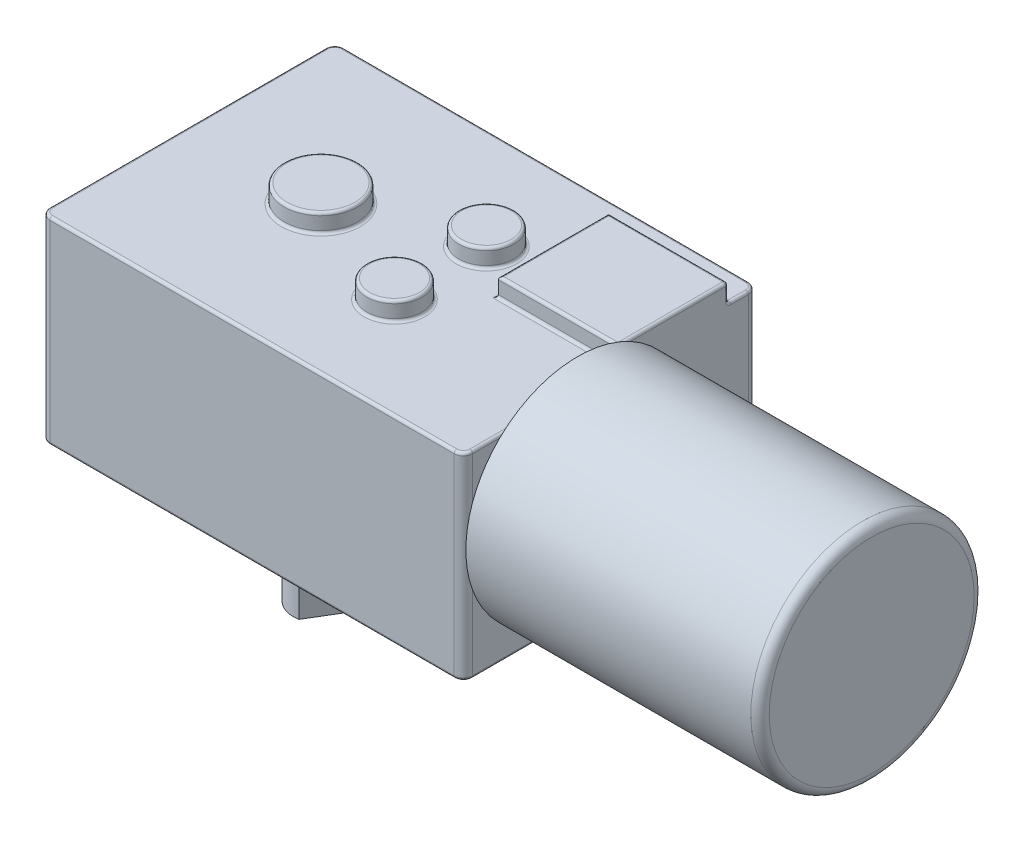
SolidWorks part; units mm, degrees
ref_plane "Front Plane" through (0, 0, 0) normal (0, 0, 1) x (1, 0, 0)
ref_plane "Top Plane" through (0, 0, 0) normal (0, 1, 0) x (1, 0, 0)
ref_plane "Right Plane" through (0, 0, 0) normal (1, 0, 0) x (0, 0, -1)
sketch "Sketch1" plane through (0, 0, 0) normal (0, 1, 0) x (1, 0, 0)
  line L1 (-23, 16) -> (23, 16)
  line L2 (-23, 16) -> (-23, -16)
  line L3 (-23, -16) -> (23, -16)
  line L4 (23, 16) -> (23, -16)
  line L5 (-23, 16) -> (23, -16) construction
  line L6 (-23, -16) -> (23, 16) construction
  point P0 (0, 0)
  dimension "D1" = 32
  dimension "D2" = 46
extrude "Boss-Extrude1" add sketch "Sketch1" along normal blind 21.5
fillet "Fillet1" radius 1 4 edges at (-23, 10.75, -16) (-23, 10.75, 16) (23, 10.75, -16) (23, 10.75, 16)
sketch "Sketch2" plane through (0, 21.5, 0) normal (0, 1, 0) x (1, 0, 0)
  line L0 (23, -15) -> (23, 15) construction
  line L1 (23, 12.8) -> (10, 12.8)
  line L2 (23, 12.8) -> (23, 0.8)
  line L3 (23, 0.8) -> (10, 0.8)
  line L4 (10, 12.8) -> (10, 0.8)
  line L5 (22, 16) -> (-22, 16) construction
  dimension "D1" = 3.2
  dimension "D2" = 12
  dimension "D3" = 13
extrude "Boss-Extrude2" add sketch "Sketch2" along normal blind 2
sketch "Sketch3" plane through (0, 21.5, 0) normal (0, 1, 0) x (1, 0, 0)
  line L0 (-23, 0) -> (-8.5, 0) construction
  line L1 (-23, 15) -> (-23, -15) construction
  line L3 (-8.5, 0) -> (4.5, 0) construction
  line L4 (4.5, 0) -> (4.5, 5) construction
  line L5 (4.5, 0) -> (4.5, -5) construction
  circle A0 centre (-8.5, 0) radius 4
  circle A1 centre (4.5, 5) radius 3
  circle A2 centre (4.5, -5) radius 3
  dimension "D2" = 8
  dimension "D3" = 6
  dimension "D4" = 6
  dimension "D1" = 14.5
  dimension "D5" = 13
  dimension "D6" = 5
  dimension "D7" = 5
extrude "Boss-Extrude3" add sketch "Sketch3" along normal blind 2
sketch "Sketch4" plane through (0, 0, 0) normal (0, -1, 0) x (1, 0, 0)
  line L0 (-23, 0) -> (-8.5, 0) construction
  line L1 (-23, -15) -> (-23, 15) construction
  line L2 (-16.4, 9.4) -> (16.4, 9.4) construction
  line L3 (16.4, 9.4) -> (16.4, -9.4) construction
  line L4 (16.4, -9.4) -> (-16.4, -9.4) construction
  line L5 (-16.4, -9.4) -> (-16.4, 9.4) construction
  line L6 (-22, 16) -> (22, 16) construction
  line L7 (23, 15) -> (23, -15) construction
  line L8 (22, -16) -> (-22, -16) construction
  circle A0 centre (-8.5, 0) radius 6.75
  circle A1 centre (-16.4, 9.4) radius 4
  circle A2 centre (-16.4, 9.4) radius 1.5
  circle A3 centre (-16.4, -9.4) radius 4
  circle A4 centre (-16.4, -9.4) radius 1.5
  circle A6 centre (16.4, -9.4) radius 1.5
  circle A7 centre (16.4, -9.4) radius 4
  circle A8 centre (16.4, 9.4) radius 1.5
  circle A9 centre (16.4, 9.4) radius 4
  circle A10 centre (4.5, 5) radius 3
  circle A11 centre (4.5, -5) radius 3
  dimension "D2" = 13.5
  dimension "D7" = 3
  dimension "D8" = 8
  dimension "D9" = 8
  dimension "D10" = 3
  dimension "D11" = 3
  dimension "D12" = 8
  dimension "D13" = 3
  dimension "D14" = 8
  dimension "D1" = 14.5
  dimension "D3" = 6.6
  dimension "D4" = 6.6
  dimension "D5" = 6.6
  dimension "D6" = 6.6
  dimension "D15" = 32.8
  dimension "D16" = 18.8
  dimension "D17" = 8.5
extrude "Boss-Extrude4" add sketch "Sketch4" along normal blind 2
fillet "Fillet2" radius 0.3 49 edges at (23, 22.5, -0.8) (23, 22.5, -12.8) (4.5, 23.5, 8) (16.5, 23.5, -0.8) (10, 23.5, -6.8) (16.5, 23.5, -12.8) (23, 23.5, -6.8) (4.5, 23.5, -2) (-8.5, 23.5, 4) (-16.4, -2, -10.9) (-16.4, -2, -13.4) (16.4, -2, -10.9) (16.4, -2, -13.4) (16.4, -2, 7.9) (16.4, -2, 5.4) (4.5, -2, -8) (4.5, -2, 2) (-16.4, -2, 7.9) (-16.4, -2, 5.4) (-22.7071, 0, 15.7071) (0, 0, 16) (22.7071, 0, 15.7071) (23, 0, 0) (22.7071, 0, -15.7071) (0, 0, -16) (-22.7071, 0, -15.7071) (-23, 0, 0) (-8.5, 0, -6.75) (-16.4, 0, 13.4) (-16.4, 0, -5.4) (16.4, 0, -5.4) (16.4, 0, 13.4) (4.5, 0, 8) (4.5, 0, -2) (23, 21.5, 7.1) (22.7071, 21.5, 15.7071) (0, 21.5, 16) (-22.7071, 21.5, 15.7071) (-23, 21.5, 0) (-22.7071, 21.5, -15.7071) (0, 21.5, -16) (22.7071, 21.5, -15.7071) (23, 21.5, -13.9) (16.5, 21.5, -12.8) (10, 21.5, -6.8) (16.5, 21.5, -0.8) (-8.5, 21.5, 4) (4.5, 21.5, -2) (4.5, 21.5, 8)
sketch "Sketch5" plane through (23, 0, 0) normal (1, 0, 0) x (0, 0, -1)
  line L0 (-3.584, 12.5) -> (0, 12.5) construction
  line L1 (0, 12.5) -> (0, 0) construction
  circle A0 centre (-3.584, 12.5) radius 12.15
  dimension "D1" = 24.3
  dimension "D2" = 12.5
extrude "Boss-Extrude5" add sketch "Sketch5" along normal blind 32
fillet "Fillet3" radius 1 1 edges at (55, 12.5, -8.566)
sketch "Sketch6" plane through (0, -2, 0) normal (0, 1, 0) x (1, 0, 0)
  circle A0 centre (-8.5, 0) radius 5
  dimension "D1" = 10
extrude "Cut-Extrude1" cut sketch "Sketch6" along normal blind 0.1
sketch "Sketch7" plane through (0, -1.9, 0) normal (0, -1, 0) x (1, 0, 0)
  circle A1 centre (-8.5, 0) radius 3
extrude "Boss-Extrude6" add sketch "Sketch7" along normal blind 14
sketch "Sketch8" plane through (0, -15.9, 0) normal (0, -1, 0) x (1, 0, 0)
  line L0 (-7.9392, 2.9471) -> (-5.6334, -0.8848)
  line L1 (-7.9392, 2.9471) -> (-4.6301, 4.9384)
  line L2 (-5.6334, -0.8848) -> (-2.3243, 1.1065)
  line L3 (-4.6301, 4.9384) -> (-2.3243, 1.1065)
  circle A0 centre (-8.5, 0) radius 3 construction
  circle A1 centre (-8.5, 0) radius 3 construction
  dimension "D1" = 2
extrude "Cut-Extrude2" cut sketch "Sketch8" against normal blind 11
